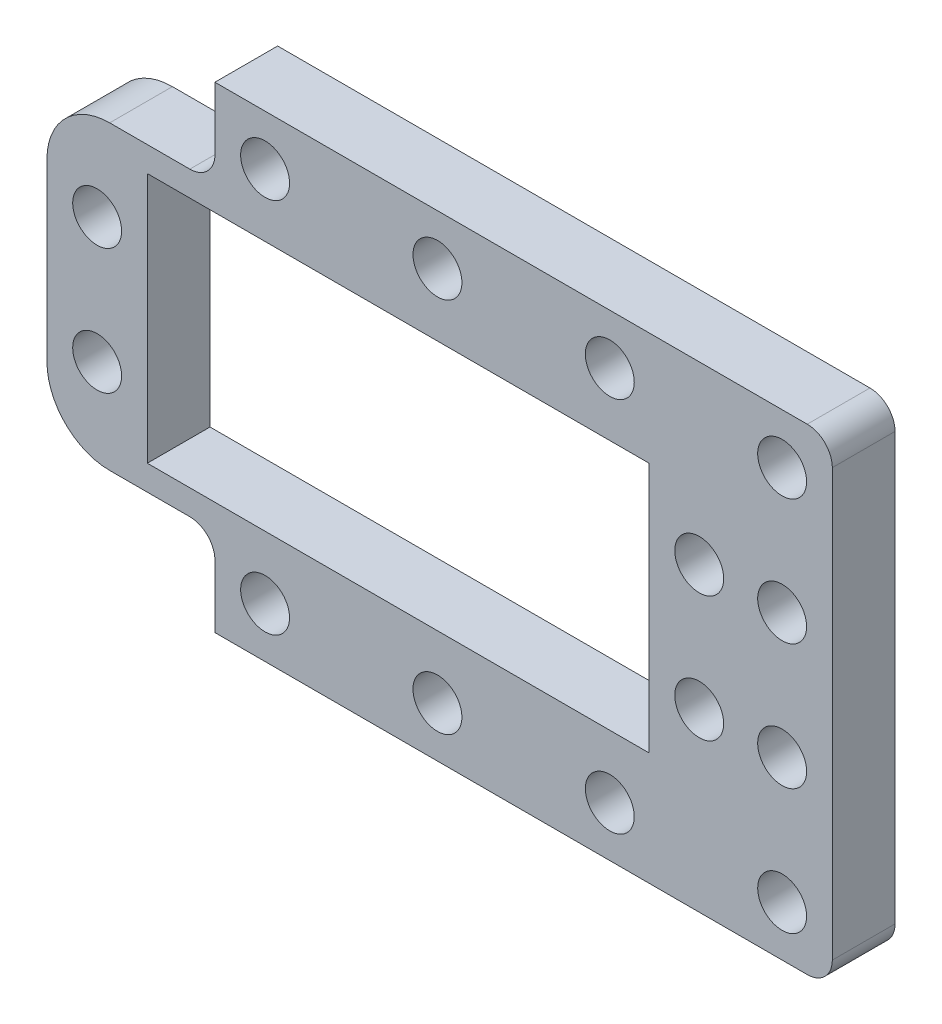
SolidWorks part; units mm, degrees
ref_plane "Front Plane" through (0, 0, 0) normal (0, 0, 1) x (1, 0, 0)
ref_plane "Top Plane" through (0, 0, 0) normal (0, 1, 0) x (1, 0, 0)
ref_plane "Right Plane" through (0, 0, 0) normal (1, 0, 0) x (0, 0, -1)
sketch "Sketch1" plane through (0, 0, 0) normal (0, 0, 1) x (1, 0, 0)
  line L0 (-34.61, -9) -> (-34.61, -29) construction
  line L1 (-2, 0) -> (-60.61, 0)
  line L3 (-2, -38) -> (-60.61, -38)
  line L4 (-62.61, -2) -> (-62.61, -36)
  line L5 (-54.61, -9) -> (-14.61, -9)
  line L6 (-54.61, -9) -> (-54.61, -29)
  line L7 (-54.61, -29) -> (-14.61, -29)
  line L8 (-14.61, -9) -> (-14.61, -29)
  line L9 (-62.61, -19) -> (0, -19) construction
  line L10 (-10.61, -24) -> (-10.61, -14) construction
  line L11 (-58.61, -24) -> (-58.61, -14) construction
  line L12 (-62.61, -4) -> (-4, -4) construction
  line L13 (-4, -4) -> (-4, -34) construction
  line L17 (0, -2) -> (0, -36)
  line L18 (0, -2) -> (0, 0) construction
  line L19 (0, 0) -> (-2, 0) construction
  arc A0 (-60.61, 0) -> (-62.61, -2) centre (-60.61, -2) ccw
  circle A4 centre (-10.61, -14) radius 1.95
  circle A5 centre (-10.61, -24) radius 1.95
  circle A6 centre (-58.61, -24) radius 1.95
  circle A7 centre (-58.61, -14) radius 1.95
  circle A8 centre (-45.22, -4) radius 1.95
  arc A9 (-2, -38) -> (0, -36) centre (-2, -36) ccw
  arc A10 (-2, 0) -> (0, -2) centre (-2, -2) cw
  circle A11 centre (-4, -4) radius 1.95
  circle A14 centre (-4, -14) radius 1.95
  circle A16 centre (-58.61, -4) radius 1.95
  circle A19 centre (-31.48, -4) radius 1.95
  circle A21 centre (-17.74, -4) radius 1.95
  arc A22 (-60.61, -38) -> (-62.61, -36) centre (-60.61, -36) cw
  circle A23 centre (-45.22, -34) radius 1.95
  circle A24 centre (-58.61, -34) radius 1.95
  circle A25 centre (-4, -34) radius 1.95
  circle A26 centre (-17.74, -34) radius 1.95
  circle A27 centre (-31.48, -34) radius 1.95
  circle A28 centre (-4, -24) radius 1.95
  point P25 (-10.61, -19)
  dimension "D5" = 2
  dimension "D6" = 3.9
  dimension "D8" = 3.9
  dimension "D9" = 3.9
  dimension "D11" = 3.9
  dimension "D2" = 2
  dimension "D15" = 4
  dimension "D16" = 3.9
  dimension "D19" = 3.9
  dimension "D24" = 3.9
  dimension "D30" = 3.9
  dimension "D32" = 3.9
  dimension "D28" = 2
  dimension "D1" = 38
  dimension "D3" = 20
  dimension "D4" = 40
  dimension "D7" = 10
  dimension "D10" = 4
  dimension "D12" = 17.39
  dimension "D13" = 62.61
  dimension "D14" = 4
  dimension "D17" = 8
  dimension "D18" = 10
  dimension "D20" = 10
  dimension "D25" = 4
  dimension "D26" = 13.74
  dimension "D27" = 13.74
other "AlignGroup1"
other "AlignGroup2"
extrude "Boss-Extrude1" add sketch "Sketch1" along normal blind 5
sketch "Sketch2" plane through (0, 0, 5) normal (0, 0, 1) x (1, 0, 0)
  line L0 (-49.22, 0) -> (-62.61, 0)
  line L1 (-49.22, 0) -> (-49.22, -7)
  line L2 (-62.61, 0) -> (-62.61, -7)
  line L3 (-49.22, -7) -> (-62.61, -7)
  line L4 (-2, 0) -> (-60.61, 0) construction
  line L6 (-62.61, -2) -> (-62.61, -36) construction
  line L8 (-49.22, -31) -> (-62.61, -31)
  line L9 (-49.22, -31) -> (-49.22, -38)
  line L10 (-62.61, -31) -> (-62.61, -38)
  line L11 (-49.22, -38) -> (-62.61, -38)
  line L12 (-60.61, -38) -> (-2, -38) construction
  dimension "D1" = 13.39
  dimension "D2" = 13.39
  dimension "D3" = 7
  dimension "D4" = 7
extrude "Cut-Extrude2" cut sketch "Sketch2" against normal through all
fillet "Fillet1" radius 2 2 edges at (-49.22, -7, 2.5) (-49.22, -31, 2.5)
fillet "Fillet2" radius 5 2 edges at (-62.61, -31, 2.5) (-62.61, -7, 2.5)
